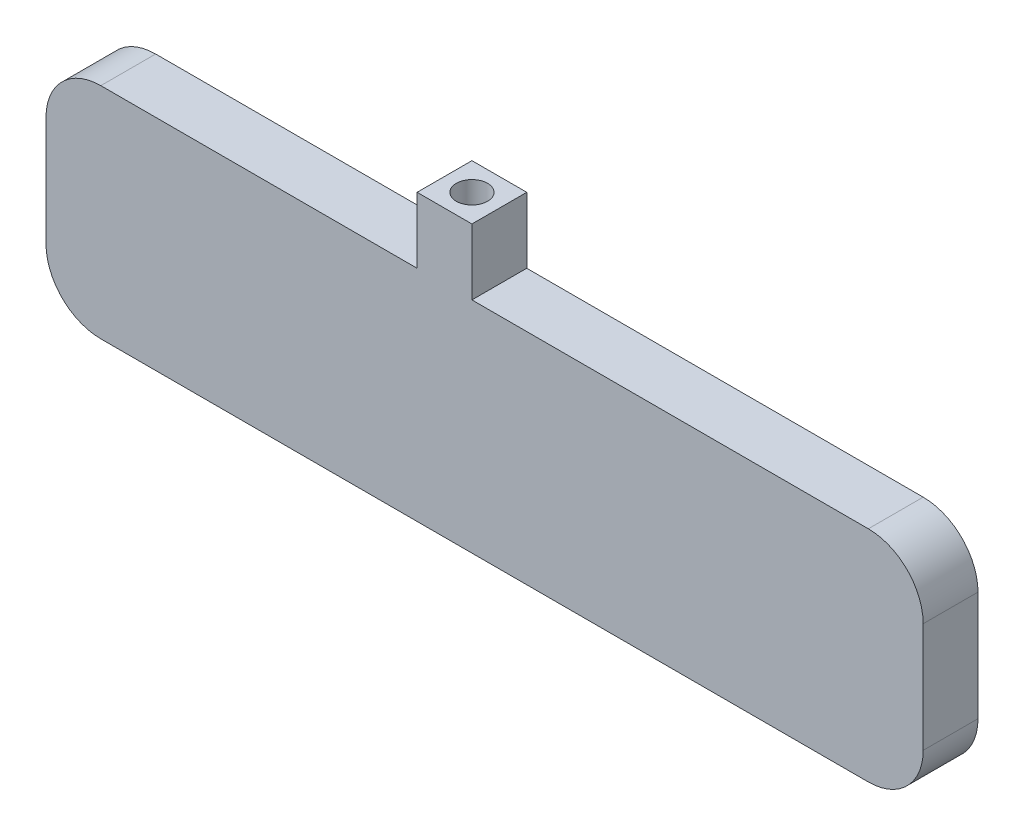
SolidWorks part; units mm, degrees
ref_plane "Front Plane" through (0, 0, 0) normal (0, 0, 1) x (1, 0, 0)
ref_plane "Top Plane" through (0, 0, 0) normal (0, 1, 0) x (1, 0, 0)
ref_plane "Right Plane" through (0, 0, 0) normal (1, 0, 0) x (0, 0, -1)
sketch "Sketch1" plane through (0, 0, 0) normal (0, 0, 1) x (1, 0, 0)
  line L1 (-40, 10) -> (40, 10)
  line L2 (-40, 10) -> (-40, -10)
  line L3 (-40, -10) -> (40, -10)
  line L4 (40, 10) -> (40, -10)
  line L5 (-40, 10) -> (40, -10) construction
  line L6 (-40, -10) -> (40, 10) construction
  point P0 (0, 0)
  dimension "D1" = 80
  dimension "D2" = 20
extrude "Boss-Extrude1" add sketch "Sketch1" along normal blind 5
fillet "Fillet1" radius 5 4 edges at (40, -10, 2.5) (40, 10, 2.5) (-40, -10, 2.5) (-40, 10, 2.5)
shell "Shell1" thickness 2
sketch "Sketch2" plane through (0, 10, 0) normal (0, 1, 0) x (1, 0, 0)
  line L0 (35, 0) -> (-35, 0) construction
  line L1 (-6.154, 0) -> (-1.154, 0)
  line L2 (-6.154, 0) -> (-6.154, -5)
  line L3 (-6.154, -5) -> (-1.154, -5)
  line L4 (-1.154, 0) -> (-1.154, -5)
  line L5 (35, -5) -> (-35, -5) construction
  dimension "D1" = 5
extrude "Boss-Extrude2" add sketch "Sketch2" along normal blind 6
sketch "Sketch3" plane through (0, 16, 0) normal (0, 1, 0) x (1, 0, 0)
  line L0 (-1.154, 0) -> (-6.154, 0) construction
  line L1 (-1.154, -5) -> (-1.154, 0) construction
  circle A0 centre (-3.654, -2.5) radius 1.425
  dimension "D1" = 2.85
  dimension "D2" = 2.5
  dimension "D3" = 2.5
extrude "Cut-Extrude1" cut sketch "Sketch3" against normal blind 4
